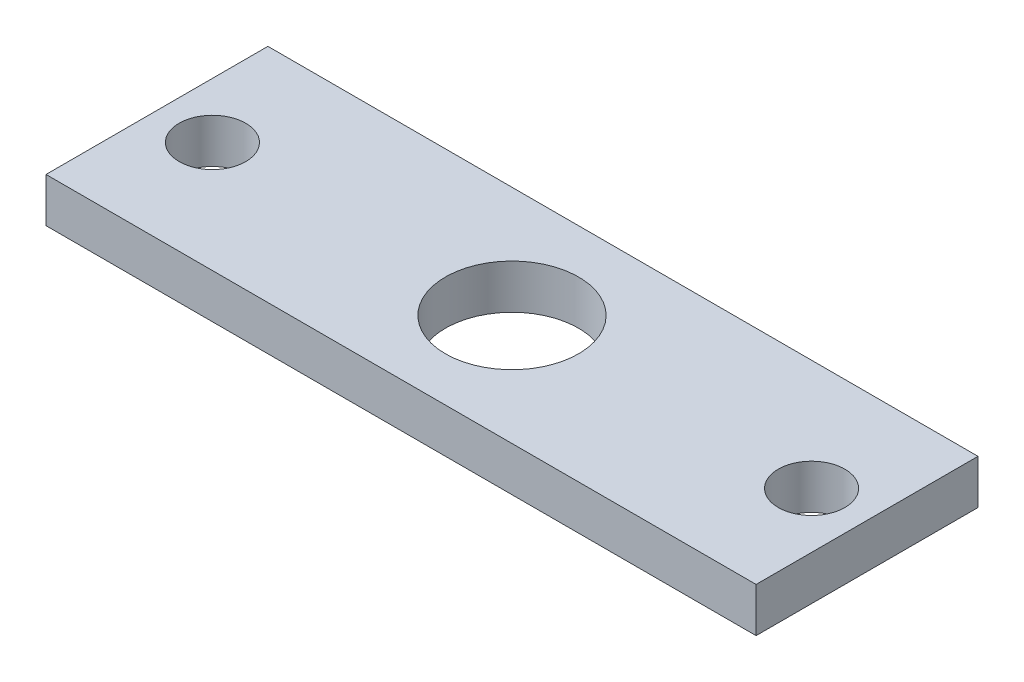
SolidWorks part; units mm, degrees
ref_plane "Front Plane" through (0, 0, 0) normal (0, 0, 1) x (1, 0, 0)
ref_plane "Top Plane" through (0, 0, 0) normal (0, 1, 0) x (1, 0, 0)
ref_plane "Right Plane" through (0, 0, 0) normal (1, 0, 0) x (0, 0, -1)
sketch "Sketch1" plane through (0, 0, 0) normal (0, 1, 0) x (1, 0, 0)
  line L1 (-25.3333, 5.1316) -> (6.6667, 5.1316)
  line L2 (-25.3333, 5.1316) -> (-25.3333, -4.8684)
  line L3 (-25.3333, -4.8684) -> (6.6667, -4.8684)
  line L4 (6.6667, 5.1316) -> (6.6667, -4.8684)
  dimension "D1" = 10
  dimension "D2" = 32
extrude "Boss-Extrude1" add sketch "Sketch1" along normal blind 2
sketch "Sketch2" plane through (0, 2, 0) normal (0, 1, 0) x (1, 0, 0)
  line L0 (-25.3333, 5.1316) -> (-25.3333, -4.8684) construction
  line L1 (-25.3333, -4.8684) -> (6.6667, -4.8684) construction
  line L3 (6.6667, 5.1316) -> (-25.3333, 5.1316) construction
  circle A0 centre (-22.8333, 0.1316) radius 1.5
  circle A1 centre (4.1667, 0.1316) radius 1.5
  circle A2 centre (-9.3333, 0.1316) radius 3
  dimension "D2" = 3
  dimension "D3" = 3
  dimension "D7" = 6
  dimension "D1" = 27
  dimension "D4" = 2.5
  dimension "D5" = 5
  dimension "D6" = 5
  dimension "D8" = 13.5
  dimension "D9" = 5
extrude "Cut-Extrude1" cut sketch "Sketch2" against normal through all
